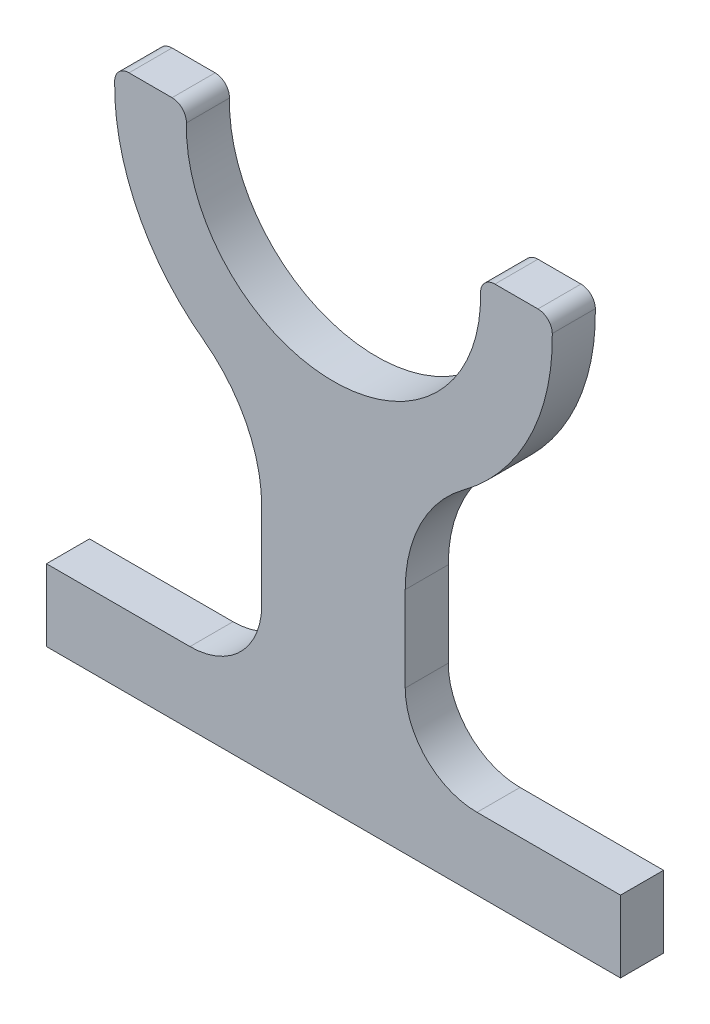
SolidWorks part; units mm, degrees
ref_plane "Front" through (0, 0, 0) normal (0, 0, 1) x (1, 0, 0)
ref_plane "Top" through (0, 0, 0) normal (0, 1, 0) x (1, 0, 0)
ref_plane "Right" through (0, 0, 0) normal (1, 0, 0) x (0, 0, -1)
sketch "Esquisse1" plane through (0, 0, 0) normal (0, 0, 1) x (1, 0, 0)
  line L0 (-40, 0) -> (40, 0)
  line L1 (-40, 0) -> (-40, 10)
  line L2 (-40, 10) -> (-20, 10)
  line L3 (-10, 20) -> (-10, 31.8767)
  line L5 (0, 150) -> (0, 72.5) construction
  line L6 (0, 150) -> (0, 72.5) construction
  line L7 (-22.4944, 75) -> (-28.4956, 75)
  line L9 (10, 20) -> (10, 31.8767)
  line L10 (40, 10) -> (20, 10)
  line L11 (40, 0) -> (40, 10)
  line L15 (28.4956, 75) -> (22.4944, 75)
  line L16 (0, 52) -> (0, 0) construction
  arc A0 (-20, 10) -> (-10, 20) centre (-20, 20) ccw
  arc A1 (-10, 31.8767) -> (-18.1188, 47.9652) centre (-30, 31.8767) ccw
  arc A2 (-18.1188, 47.9652) -> (-30.4953, 73.0351) centre (0, 72.5) cw
  arc A3 (-20.4949, 72.9556) -> (20.4949, 72.9556) centre (0, 72.5) ccw
  arc A4 (18.1188, 47.9652) -> (30.4953, 73.0351) centre (0, 72.5) ccw
  arc A5 (10, 31.8767) -> (18.1188, 47.9652) centre (30, 31.8767) cw
  arc A6 (20, 10) -> (10, 20) centre (20, 20) cw
  arc A7 (22.4944, 75) -> (20.4949, 72.9556) centre (22.4944, 73) ccw
  arc A8 (-20.4949, 72.9556) -> (-22.4944, 75) centre (-22.4944, 73) ccw
  arc A9 (30.4953, 73.0351) -> (28.4956, 75) centre (28.4956, 73) ccw
  arc A10 (-30.4953, 73.0351) -> (-28.4956, 75) centre (-28.4956, 73) cw
  point P4 (0, 0)
  point P31 (-20.347, 75)
  dimension "D1" = 20.5
  dimension "D5" = 10
  dimension "D6" = 20
  dimension "D10" = 52
  dimension "D2" = 10
  dimension "D11" = 2
  dimension "D12" = 2
  dimension "D3" = 10
  dimension "D4" = 10
  dimension "D7" = 75
  dimension "D8" = 80
  dimension "D9" = 150
extrude "Boss.-Extru.1" add sketch "Esquisse1" along normal mid plane 6
